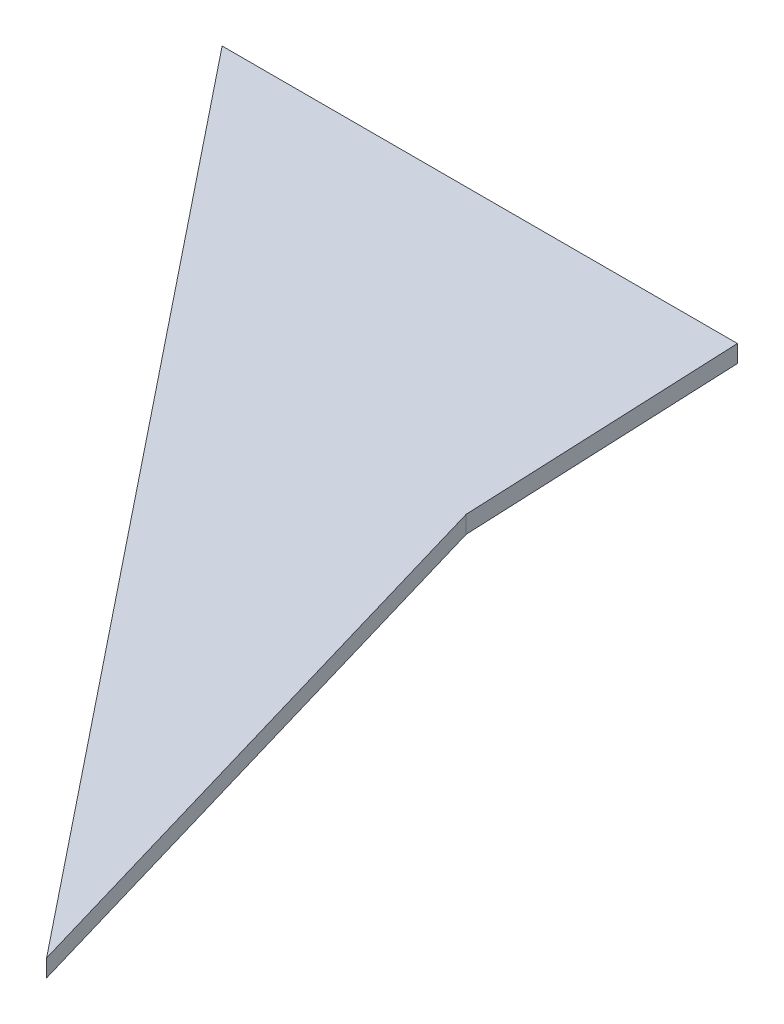
SolidWorks part; units mm, degrees
ref_plane "Plan de face" through (0, 0, 0) normal (0, 0, 1) x (1, 0, 0)
ref_plane "Plan de dessus" through (0, 0, 0) normal (0, 1, 0) x (1, 0, 0)
ref_plane "Plan de droite" through (0, 0, 0) normal (1, 0, 0) x (0, 0, -1)
sketch "Esquisse1" plane through (0, 0, 0) normal (0, 1, 0) x (1, 0, 0)
  line L0 (0, 0) -> (80.8345, -101.0504)
  line L1 (80.8345, -101.0504) -> (60.7478, -32.6425)
  line L2 (60.7478, -32.6425) -> (59.3343, 0)
  line L3 (59.3343, 0) -> (0, 0)
  point P4 (0, 0)
extrude "Boss.-Extru.1" add sketch "Esquisse1" along normal blind 2
